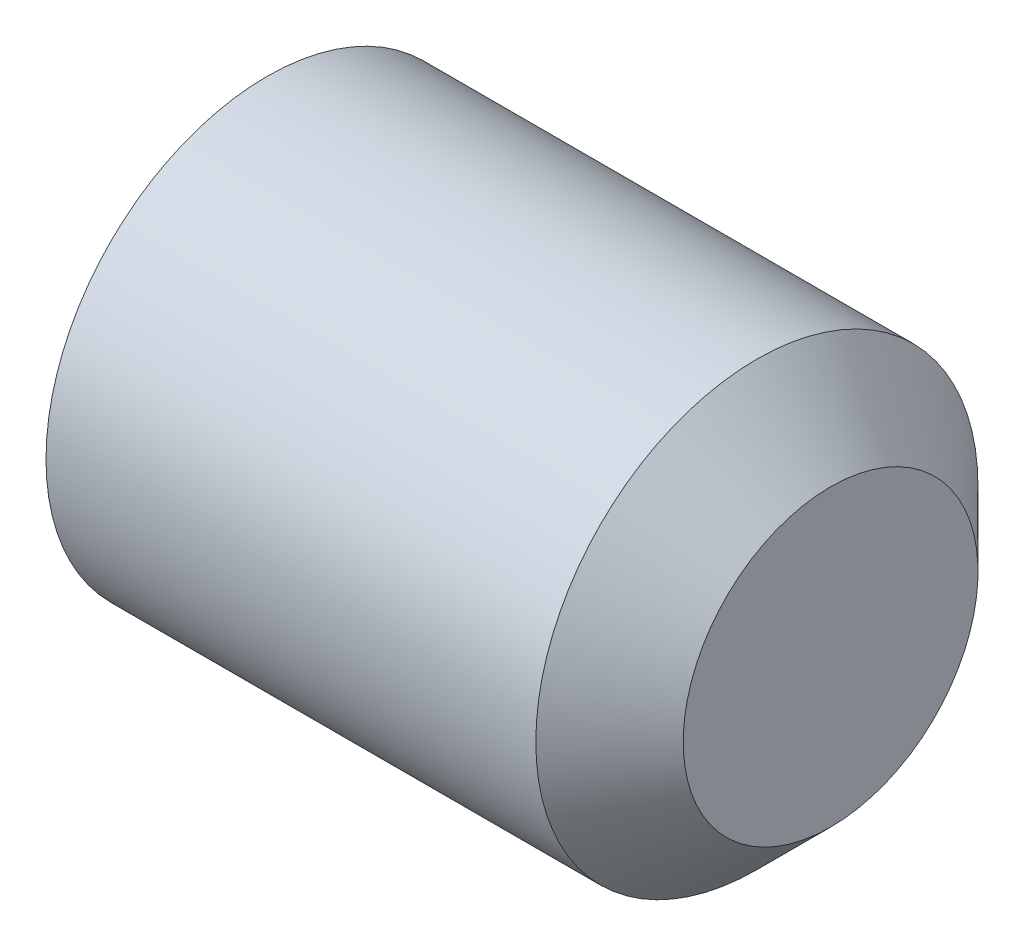
SolidWorks part; units mm, degrees
ref_plane "Front Plane" through (0, 0, 0) normal (0, 0, 1) x (1, 0, 0)
ref_plane "Top Plane" through (0, 0, 0) normal (0, 1, 0) x (1, 0, 0)
ref_plane "Right Plane" through (0, 0, 0) normal (1, 0, 0) x (0, 0, -1)
ref_plane "Plane1" through (0, 0, 0) normal (0, 0, 1) x (1, 0, 0)
sketch "Sketch1" plane through (0, 0, 0) normal (0, 0, 1) x (1, 0, 0)
  line L0 (4, 0) -> (4, -1)
  line L1 (4, -1) -> (3.5, -1.5)
  line L2 (3.5, -1.5) -> (0.177, -1.5)
  line L3 (0.177, -1.5) -> (0, -1.1935)
  line L4 (0, -1.1935) -> (0, -0.866)
  line L5 (0, -0.866) -> (0.5, 0)
  line L6 (0.5, 0) -> (4, 0)
  line L7 (0.5, 0) -> (4, 0) construction
revolve "Revolve1" add sketch "Sketch1" angle 360 about L7
ref_plane "Plane2" through (0, 0, 0) normal (1, 0, 0) x (0, 0, -1)
sketch "Sketch2" plane through (0, 0, 0) normal (1, 0, 0) x (0, 0, -1)
  line L0 (-0.866, 0) -> (-0.433, -0.75)
  line L1 (-0.433, -0.75) -> (0.433, -0.75)
  line L2 (0.433, -0.75) -> (0.866, 0)
  line L3 (0.866, 0) -> (0.433, 0.75)
  line L4 (0.433, 0.75) -> (-0.433, 0.75)
  line L5 (-0.433, 0.75) -> (-0.866, 0)
extrude "Cut-Extrude1" cut sketch "Sketch2" along normal blind 1.2
